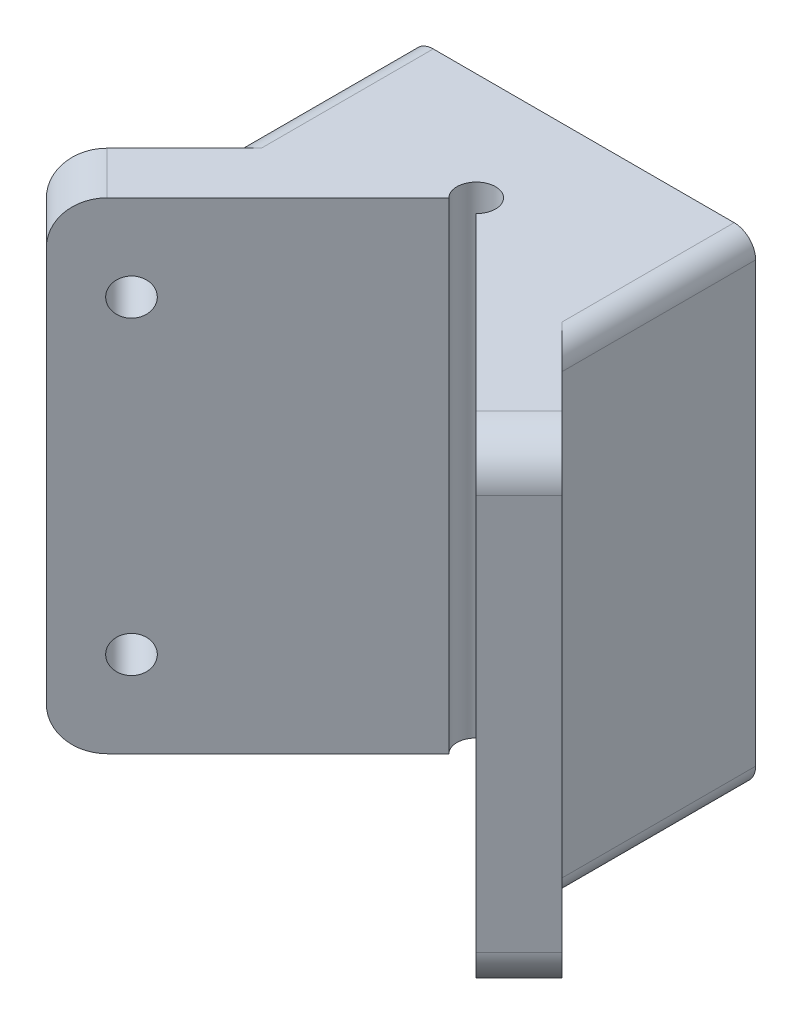
SolidWorks part; units mm, degrees
ref_plane "Plan de face" through (0, 0, 0) normal (0, 0, 1) x (1, 0, 0)
ref_plane "Plan de dessus" through (0, 0, 0) normal (0, 1, 0) x (1, 0, 0)
ref_plane "Plan de droite" through (0, 0, 0) normal (1, 0, 0) x (0, 0, -1)
sketch "Esquisse1" plane through (0, 0, 0) normal (0, 0, 1) x (1, 0, 0)
  line L1 (-40, 56) -> (40, 56)
  line L2 (-40, 56) -> (-40, -56)
  line L3 (-40, -56) -> (40, -56)
  line L4 (40, 56) -> (40, -56)
  line L5 (0, -56) -> (0, 56) construction
  line L6 (-40, 0) -> (40, 0) construction
  point P0 (0, 0)
  dimension "D1" = 80
  dimension "D2" = 112
extrude "Boss.-Extru.1" add sketch "Esquisse1" along normal blind 100
sketch "Esquisse4" plane through (0, 0, 0) normal (0, 0, 1) x (1, 0, 0)
  line L0 (-32, 67.4639) -> (-32, -70.1357) construction
  line L1 (-40, 56) -> (-40, -56) construction
  line L2 (32, 63.8378) -> (32, -66.128) construction
  line L3 (40, -56) -> (40, 56) construction
  line L4 (40, 56) -> (-40, 56) construction
  line L5 (-40, -56) -> (40, -56) construction
  circle A0 centre (-32, 47.9977) radius 2.5
  circle A1 centre (32, 48) radius 2.5
  circle A2 centre (-32, -48) radius 2.5
  circle A3 centre (32, -48) radius 2.5
  dimension "D3" = 5
  dimension "D5" = 5
  dimension "D7" = 5
  dimension "D9" = 5
  dimension "D10" = 8
  dimension "D1" = 8
  dimension "D2" = 8
  dimension "D4" = 8.0023
  dimension "D6" = 8
  dimension "D8" = 8
extrude "Enlèv. mat.-Extru.2" cut sketch "Esquisse4" along normal up to surface (100 mm away) and the other way through all contours A2 | A1 | A0 | A3 up to face at (0, 0, 100)
ref_plane "Plan10" through (0, 56, 0) normal (0, 1, 0) x (1, 0, 0)
sketch "Esquisse11" plane through (0, 56, 0) normal (0, 1, 0) x (1, 0, 0)
  line L0 (-57.7572, -5) -> (65.2879, -5) construction
  line L1 (40, 0) -> (-40, 0) construction
  line L2 (0, 0) -> (0, -103.5009) construction
  line L3 (-60, 3.5009) -> (-60, -105.3145) construction
  line L4 (-82.0314, -65) -> (65.2879, -65) construction
  line L5 (-60, -65) -> (0, -5)
  line L6 (0, -5) -> (60, -65)
  line L7 (60, -65) -> (-60, -65)
  dimension "D1" = 5
  dimension "D2" = 60
  dimension "D3" = 60
  dimension "D4" = 90
extrude "Boss.-Extru.2" add sketch "Esquisse11" against normal blind 112
sketch "Esquisse13" plane through (0, 56, 0) normal (0, 1, 0) x (1, 0, 0)
  line L0 (-60, -65) -> (-40, -85)
  line L1 (-40, -100) -> (-40, -65) construction
  line L2 (-40, -85) -> (-40, -65)
  line L3 (-60, -65) -> (-40, -65) construction
  line L4 (-40, -65) -> (-60, -65)
  line L6 (60, -65) -> (40, -85)
  line L7 (40, -100) -> (40, -65) construction
  line L8 (40, -85) -> (40, -65)
  line L9 (40, -65) -> (60, -65)
  line L10 (60, -65) -> (40, -45) construction
  dimension "D1" = 90
extrude "Boss.-Extru.4" add sketch "Esquisse13" against normal blind 112
sketch "Esquisse14" plane through (0, 56, 0) normal (0, 1, 0) x (1, 0, 0)
  line L0 (0, 8.851) -> (0, -109.6183) construction
  line L1 (-60, -65) -> (-40, -85) construction
  line L2 (-50, -75) -> (57.0095, -75) construction
  line L3 (-78.0332, -25) -> (57.0095, -25) construction
  line L4 (-50, -75) -> (0, -25)
  line L5 (0, -25) -> (50, -75)
  line L6 (50, -75) -> (40, -85)
  line L7 (40, -85) -> (40, -100)
  line L8 (40, -100) -> (-40, -100)
  line L9 (-40, -100) -> (-40, -85)
  line L10 (-40, -85) -> (-50, -75)
  dimension "D1" = 50
extrude "Enlèv. mat.-Extru.6" cut sketch "Esquisse14" against normal blind 112
ref_plane "Plan14" through (-2.5, 0, 2.5) normal (0.7071, 0, -0.7071) x (-0.7071, 0, -0.7071)
sketch "Esquisse15" plane through (-2.5, 0, 2.5) normal (0.7071, 0, -0.7071) x (-0.7071, 0, -0.7071)
  line L0 (-74.3883, 61.509) -> (-74.3883, -65.9215) construction
  line L1 (-88.3883, -56) -> (-88.3883, 56) construction
  line L3 (-88.3883, 56) -> (-60.1041, 56) construction
  line L4 (-88.3883, -56) -> (-60.1041, -56) construction
  circle A0 centre (-74.3883, 36) radius 4.25
  circle A1 centre (-74.3883, -36) radius 4.25
  dimension "D2" = 8.5
  dimension "D3" = 8.5
  dimension "D1" = 14
  dimension "D4" = 20
  dimension "D5" = 20
ref_plane "Plan15" through (2.5, 0, 2.5) normal (-0.7071, 0, -0.7071) x (-0.7071, 0, 0.7071)
sketch "Esquisse16" plane through (2.5, 0, 2.5) normal (-0.7071, 0, -0.7071) x (-0.7071, 0, 0.7071)
  line L0 (74.3883, 58.1727) -> (74.3883, -66.4089) construction
  line L1 (88.3883, -56) -> (88.3883, 56) construction
  line L2 (60.1041, 56) -> (88.3883, 56) construction
  line L3 (60.1041, -56) -> (88.3883, -56) construction
  circle A0 centre (74.3883, 36) radius 4.25
  circle A1 centre (74.3883, -36) radius 4.25
  dimension "D2" = 8.5
  dimension "D3" = 8.5
  dimension "D1" = 14
  dimension "D4" = 20
  dimension "D5" = 20
extrude "Enlèv. mat.-Extru.7" cut sketch "Esquisse16" against normal blind 112
extrude "Enlèv. mat.-Extru.10" cut sketch "Esquisse15" against normal blind 112 contours A1 | A0
fillet "Congé1" radius 10 4 edges at (55, -56, 70) (55, 56, 70) (-55, -56, 70) (-55, 56, 70)
fillet "Congé2" radius 5 4 edges at (-40, 56, 22.5) (40, 56, 22.5) (-40, -56, 22.5) (40, -56, 22.5)
ref_plane "Plan16" through (0, 56, 0) normal (0, 1, 0) x (1, 0, 0)
sketch "Esquisse17" plane through (0, 56, 0) normal (0, 1, 0) x (1, 0, 0)
  circle A0 centre (0, -25) radius 4.5
  dimension "D1" = 9
extrude "Enlèv. mat.-Extru.12" cut sketch "Esquisse17" against normal blind 112
